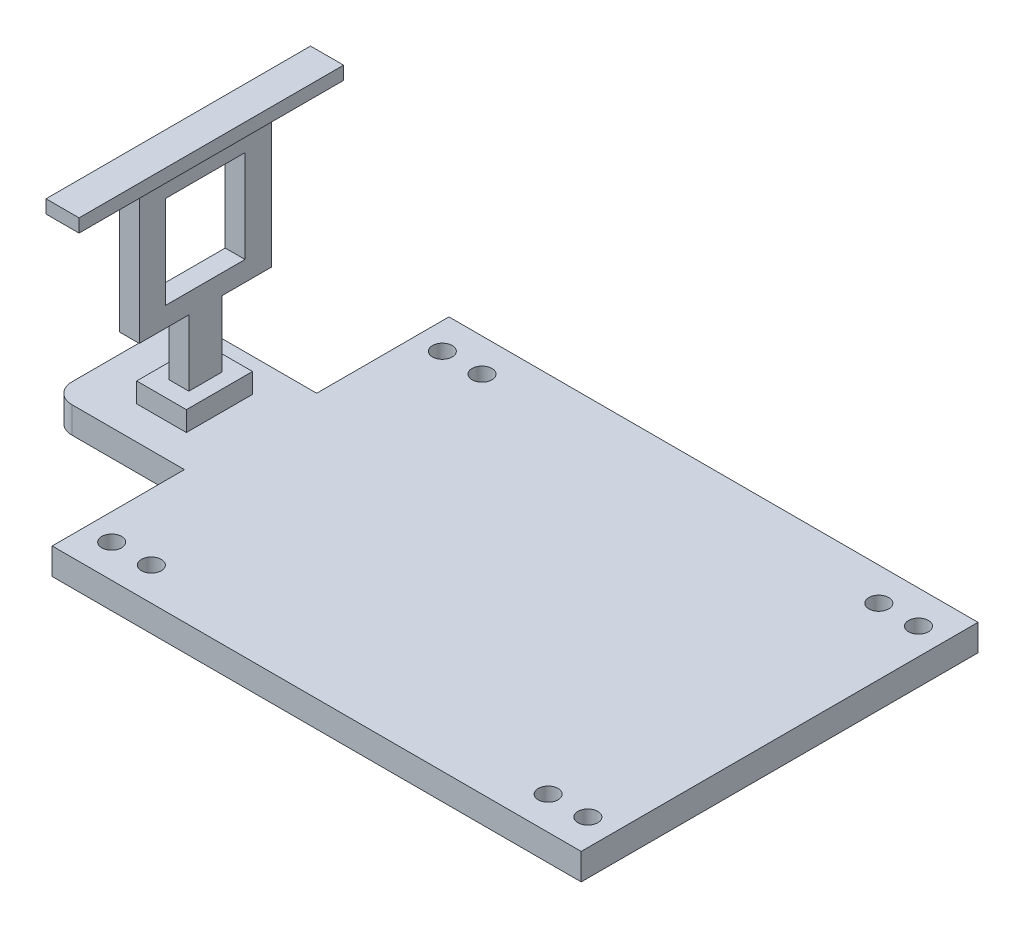
SolidWorks part; units mm, degrees
ref_plane "Front Plane" through (0, 0, 0) normal (0, 0, 1) x (1, 0, 0)
ref_plane "Top Plane" through (0, 0, 0) normal (0, 1, 0) x (1, 0, 0)
ref_plane "Right Plane" through (0, 0, 0) normal (1, 0, 0) x (0, 0, -1)
sketch "Sketch1" plane through (0, 0, 0) normal (0, 1, 0) x (1, 0, 0)
  line L0 (-54.069, 20) -> (-54.069, 40)
  line L1 (-54.069, 40) -> (25.931, 40)
  line L2 (25.931, 40) -> (25.931, -20)
  line L3 (25.931, -20) -> (-54.069, -20)
  line L4 (-54.069, -20) -> (-54.069, 0)
  line L5 (-54.069, 0) -> (-71.069, 0)
  line L6 (-74.069, 3) -> (-74.069, 17)
  line L7 (-71.069, 20) -> (-54.069, 20)
  arc A0 (-71.069, 20) -> (-74.069, 17) centre (-71.069, 17) ccw
  arc A1 (-74.069, 3) -> (-71.069, 0) centre (-71.069, 3) ccw
  circle A2 centre (-50.069, 35) radius 1.5
  circle A3 centre (-44.069, 35) radius 1.5
  circle A4 centre (-50.069, -15) radius 1.5
  circle A5 centre (-44.069, -15) radius 1.5
  circle A6 centre (21.931, -15) radius 1.5
  circle A7 centre (15.931, -15) radius 1.5
  circle A8 centre (15.931, 35) radius 1.5
  circle A9 centre (21.931, 35) radius 1.5
  dimension "D6" = 10
  dimension "D2" = 5
  dimension "D4" = 5
  dimension "D7" = 4
  dimension "D8" = 5
  dimension "D9" = 4
  dimension "D10" = 5
  dimension "D11" = 10
  dimension "D12" = 5
  dimension "D13" = 5
  dimension "D14" = 10
  dimension "D15" = 4
  dimension "D16" = 5
  dimension "D17" = 10
  dimension "D18" = 5
  dimension "D19" = 4
  dimension "D1" = 80
  dimension "D3" = 60
  dimension "D5" = 20
extrude "Boss-Extrude2" add sketch "Sketch1" along normal blind 4
sketch "Sketch2" plane through (0, 4, 0) normal (0, 1, 0) x (1, 0, 0)
  line L0 (-54.069, 20) -> (-71.069, 20) construction
  line L1 (-66.2909, 15) -> (-58.7709, 15)
  line L2 (-66.2909, 15) -> (-66.2909, 5)
  line L3 (-66.2909, 5) -> (-58.7709, 5)
  line L4 (-58.7709, 15) -> (-58.7709, 5)
  line L5 (-71.069, 0) -> (-54.069, 0) construction
  point P4 (-62.569, 20)
  point P7 (-62.569, 0)
  dimension "D1" = 5
  dimension "D2" = 5
  dimension "D3" = 10
extrude "Boss-Extrude3" add sketch "Sketch2" along normal blind 3
sketch "Sketch4" plane through (0, 0, 0) normal (1, 0, 0) x (0, 0, -1)
  line L0 (7.603, 7) -> (7.603, 17)
  line L1 (5, 7) -> (15, 7) construction
  line L2 (7.603, 17) -> (0.103, 17)
  line L3 (0.103, 17) -> (0.103, 37)
  line L4 (0.103, 37) -> (20.103, 37)
  line L5 (20.103, 37) -> (20.103, 17)
  line L6 (20.103, 17) -> (12.603, 17)
  line L7 (12.603, 17) -> (12.603, 7)
  line L8 (12.603, 7) -> (7.603, 7)
  line L9 (4.103, 34) -> (4.103, 20)
  line L10 (15, 7) -> (5, 7) construction
  line L11 (5, 4) -> (15, 4) construction
  line L12 (4.103, 20) -> (16.103, 20)
  line L13 (16.103, 20) -> (16.103, 34)
  line L14 (16.103, 34) -> (4.103, 34)
  point P12 (10, 4)
  dimension "D1" = 10
  dimension "D2" = 10
  dimension "D3" = 20
  dimension "D4" = 20
  dimension "D5" = 20
  dimension "D6" = 5
  dimension "D7" = 7.5
  dimension "D8" = 10
  dimension "D9" = 3
  dimension "D10" = 3
  dimension "D11" = 3
  dimension "D12" = 4
  dimension "D13" = 4
extrude "Boss-Extrude4" add sketch "Sketch4" against normal blind 64
sketch "Sketch5" plane through (0, 0, 0) normal (1, 0, 0) x (0, 0, -1)
  line L0 (0.103, 37) -> (0.103, 17)
  line L1 (0.103, 17) -> (7.603, 17)
  line L2 (7.603, 17) -> (7.603, 7)
  line L3 (7.603, 17) -> (7.603, 7) construction
  line L4 (7.603, 7) -> (12.603, 7) construction
  line L5 (7.603, 7) -> (12.603, 7)
  line L6 (12.603, 7) -> (12.603, 17) construction
  line L7 (12.603, 7) -> (12.603, 17)
  line L8 (12.603, 17) -> (20.103, 17)
  line L9 (20.103, 17) -> (20.103, 37) construction
  line L10 (12.603, 17) -> (20.103, 17) construction
  line L11 (20.103, 17) -> (20.103, 37)
  line L12 (20.103, 37) -> (0.103, 37)
extrude "Cut-Extrude1" cut sketch "Sketch5" against normal blind 61
sketch "Sketch6" plane through (0, 37, 0) normal (0, 1, 0) x (1, 0, 0)
  line L0 (-64, 20.103) -> (-64, 0.103) construction
  line L1 (-65, 30) -> (-60, 30)
  line L2 (-65, 30) -> (-65, -10)
  line L3 (-65, -10) -> (-60, -10)
  line L4 (-60, 30) -> (-60, -10)
  line L5 (-71.069, 0) -> (-54.069, 0) construction
  point P6 (-62.569, 0)
  dimension "D1" = 40
  dimension "D2" = 5
  dimension "D3" = 1
  dimension "D4" = 10
extrude "Boss-Extrude5" add sketch "Sketch6" along normal blind 2
